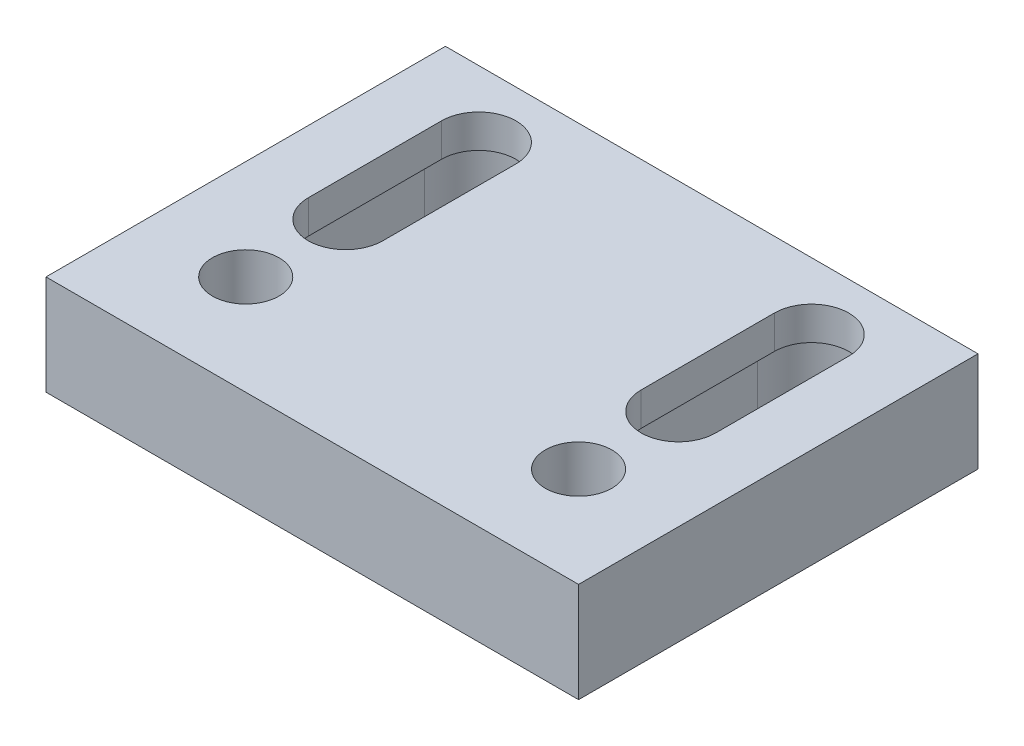
SolidWorks part; units mm, degrees
material "AISI 1018 Steel Cold Rolled"
ref_plane "Plane1" through (0, 0, 0) normal (0, 0, 1) x (1, 0, 0)
ref_plane "Plane2" through (0, 0, 0) normal (0, 1, 0) x (1, 0, 0)
ref_plane "Plane3" through (0, 0, 0) normal (1, 0, 0) x (0, 0, -1)
sketch "Sketch1" plane through (0, 0, 0) normal (0, 1, 0) x (1, 0, 0)
  line L0 (57.15, 76.2) -> (57.15, 0) construction
  line L1 (0, 0) -> (114.3, 0)
  line L2 (0, 0) -> (0, 76.2)
  line L3 (0, 76.2) -> (114.3, 76.2)
  line L4 (114.3, 0) -> (114.3, 76.2)
  line L5 (96.012, 63.5) -> (96.012, 38.1)
  line L6 (18.288, 63.5) -> (18.288, 38.1)
  line L7 (32.512, 63.5) -> (32.512, 38.1)
  line L8 (81.788, 63.5) -> (81.788, 38.1)
  line L9 (18.288, 50.8) -> (32.512, 50.8) construction
  line L10 (96.012, 50.8) -> (81.788, 50.8) construction
  arc A0 (32.512, 63.5) -> (18.288, 63.5) centre (25.4, 63.5) ccw
  arc A1 (18.288, 38.1) -> (32.512, 38.1) centre (25.4, 38.1) ccw
  arc A4 (96.012, 38.1) -> (81.788, 38.1) centre (88.9, 38.1) cw
  arc A5 (81.788, 63.5) -> (96.012, 63.5) centre (88.9, 63.5) cw
  dimension "D3" = 14.224
  dimension "D7" = 63.5
  dimension "D1" = 76.2
  dimension "D2" = 114.3
  dimension "D4" = 25.4
  dimension "D5" = 25.4
  dimension "D8" = 25.4
extrude "Base-Extrude" add sketch "Sketch1" along normal blind 19.05
hole_wizard "1/2-20 Tapped Hole1" positions "Sketch3" profile "Sketch2" tap size "1/2-20" standard "Ansi Inch" end condition through all
sketch "Sketch3" plane through (0, 19.05, 0) normal (0, 1, 0) x (-1, 0, 0)
  line L0 (0, 0) -> (-114.3, 0) construction
  line L2 (-114.3, 0) -> (-114.3, -76.2) construction
  point P0 (-25.4, -19.05)
  point P1 (-88.9, -19.05)
  dimension "D1" = 19.05
  dimension "D2" = 19.05
  dimension "D3" = 88.9
  dimension "D4" = 25.4
sketch "Sketch2" plane through (25.4, 19.05, -19.05) normal (1, 0, 0) x (0, 0, 1)
  line L0 (0, 0) -> (0, 19.05)
  line L1 (0, 19.05) -> (6.35, 19.05)
  line L2 (6.35, 19.05) -> (6.35, 0)
  line L5 (6.35, 0) -> (0, 0)
  line L11 (0, -6.35) -> (0, 107.95) construction
  dimension "Thread Major Dia." = 12.7
  dimension "Thru Tap Drill Depth" = 19.05
ref_plane "Plane4" through (133.35, 0, 0) normal (1, 0, 0) x (0, 0, -1)
sketch "Sketch4" plane through (0, 0, 0) normal (0, -1, 0) x (1, 0, 0)
  line L0 (0, -76.2) -> (0, 0) construction
  line L4 (15.0749, -63.5) -> (15.0749, -38.1)
  line L5 (35.7251, -38.1) -> (35.7251, -63.5)
  arc A4 (35.7251, -38.1) -> (15.0749, -38.1) centre (25.4, -38.1) ccw
  arc A5 (15.0749, -63.5) -> (35.7251, -63.5) centre (25.4, -63.5) ccw
  dimension "D1" = 25.4
extrude "Cut-Extrude1" cut sketch "Sketch4" against normal blind 12.7
sketch "Sketch5" plane through (0, 0, 0) normal (0, -1, 0) x (1, 0, 0)
  line L4 (99.2251, -38.1) -> (99.2251, -63.5)
  line L5 (78.5749, -63.5) -> (78.5749, -38.1)
  arc A4 (78.5749, -63.5) -> (99.2251, -63.5) centre (88.9, -63.5) ccw
  arc A5 (99.2251, -38.1) -> (78.5749, -38.1) centre (88.9, -38.1) ccw
extrude "Cut-Extrude2" cut sketch "Sketch5" against normal blind 12.7
sketch "Sketch7" plane through (0, 0, 0) normal (0, -1, 0) x (1, 0, 0)
  line L2 (107.95, 0) -> (107.95, -76.2)
  line L3 (107.95, 15.9678) -> (107.95, -89.1916)
  dimension "D1" = 6.35
sketch "Sketch8" plane through (0, 0, 0) normal (0, -1, 0) x (1, 0, 0)
  line L2 (6.35, -76.2) -> (6.35, 0)
  line L3 (6.35, -87.7035) -> (6.35, 17.952)
  dimension "D1" = 6.35
extrude "Cut-Extrude3" cut sketch "Sketch7" against normal through all and the other way through all
extrude "Cut-Extrude4" cut sketch "Sketch8" against normal through all and the other way through all
